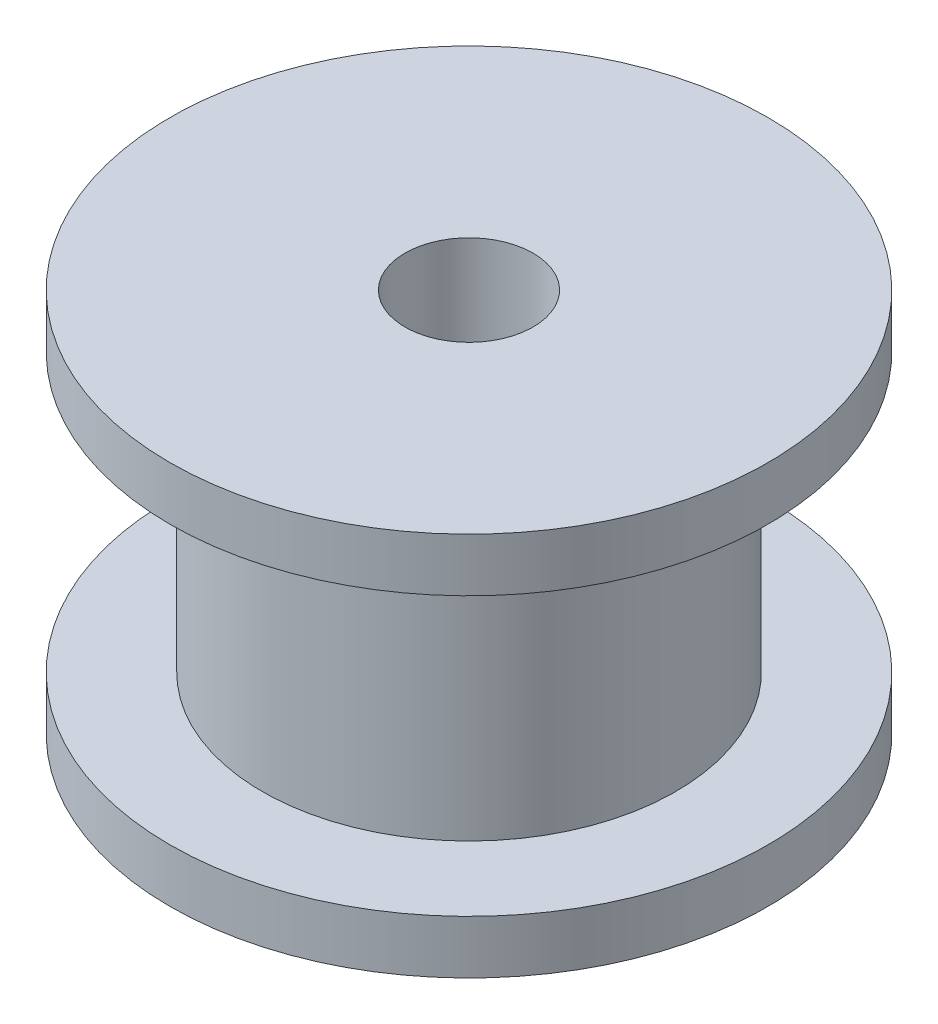
SolidWorks part; units mm, degrees
ref_plane "Plano frontal" through (0, 0, 0) normal (0, 0, 1) x (1, 0, 0)
ref_plane "Plano superior" through (0, 0, 0) normal (0, 1, 0) x (1, 0, 0)
ref_plane "Plano direito" through (0, 0, 0) normal (1, 0, 0) x (0, 0, -1)
sketch "Esboço1" plane through (0, 0, 0) normal (0, 0, 1) x (1, 0, 0)
  line L0 (1.5, 9) -> (7, 9)
  line L1 (7, 9) -> (7, 7.75)
  line L2 (7, 7.75) -> (4.84, 7.75)
  line L3 (4.84, 7.75) -> (4.84, 1.25)
  line L4 (4.84, 1.25) -> (7, 1.25)
  line L5 (7, 1.25) -> (7, 0)
  line L6 (7, 0) -> (1.5, 0)
  line L7 (1.5, 0) -> (1.5, 9)
  line L8 (0, 0) -> (0, 9.423) construction
  dimension "D1" = 14
  dimension "D2" = 3
  dimension "D3" = 9
  dimension "D4" = 6.5
  dimension "D5" = 9.68
revolve "Revolução1" add sketch "Esboço1" angle 360 about L8
